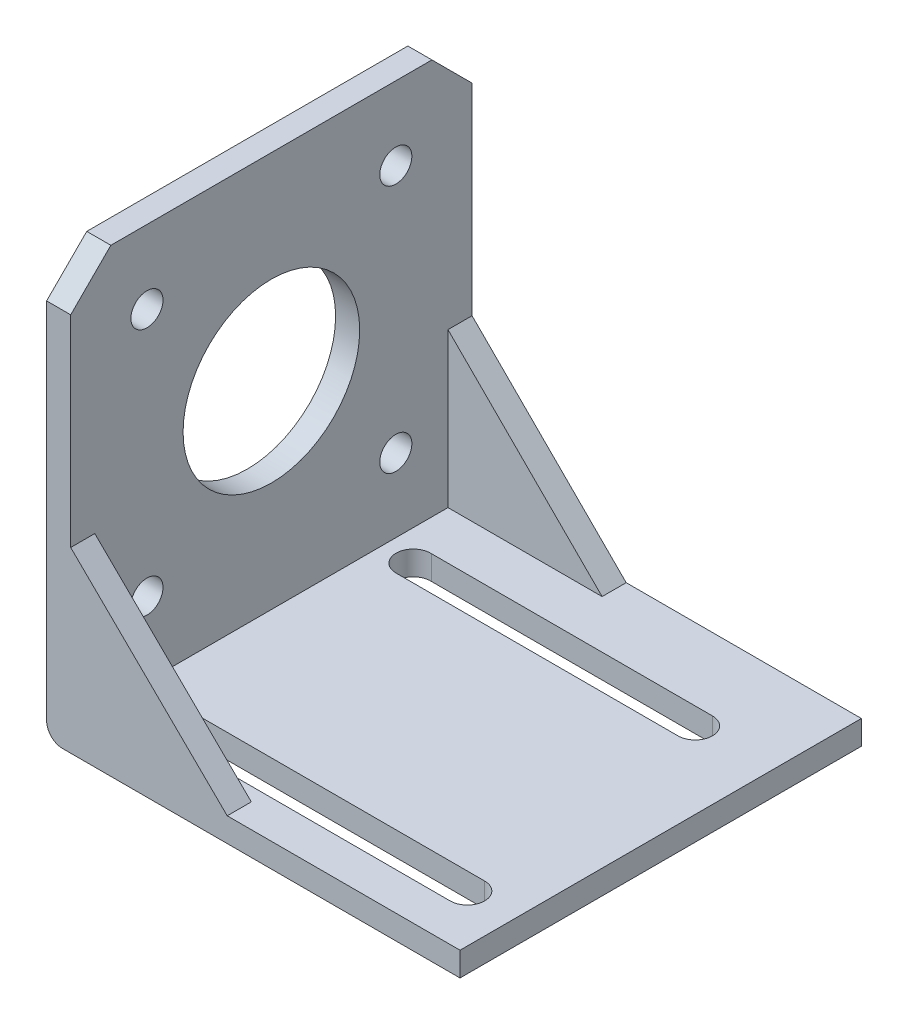
SolidWorks part; units mm, degrees
ref_plane "Front Plane" through (0, 0, 0) normal (0, 0, 1) x (1, 0, 0)
ref_plane "Top Plane" through (0, 0, 0) normal (0, 1, 0) x (1, 0, 0)
ref_plane "Right Plane" through (0, 0, 0) normal (1, 0, 0) x (0, 0, -1)
sketch "Sketch1" plane through (0, 0, 0) normal (0, 0, 1) x (1, 0, 0)
  line L0 (0, 0) -> (0, 49.3)
  line L1 (0, 49.3) -> (-3, 49.3)
  line L2 (-3, 49.3) -> (-3, -3)
  line L3 (-3, -3) -> (48.5, -3)
  line L4 (48.5, -3) -> (48.5, 0)
  line L5 (48.5, 0) -> (0, 0)
  dimension "D1" = 3
  dimension "D2" = 3
  dimension "D3" = 51.5
  dimension "D4" = 52.3
extrude "Boss-Extrude1" add sketch "Sketch1" along normal blind 50
sketch "Sketch8" plane through (0, 0, 50) normal (0, 0, 1) x (1, 0, 0)
  line L0 (0, 0) -> (0, 49.3) construction
  line L1 (48.5, 0) -> (0, 0) construction
  line L2 (-3, -3) -> (48.5, -3) construction
  line L3 (-3, 49.3) -> (-3, -3) construction
  line L4 (0, 19.2) -> (19.5, 0)
  point P0 (0, 19.2)
  point P1 (19.5, 0)
  dimension "D1" = 22.2
  dimension "D2" = 22.5
rib "Rib1" sketch "Sketch8" sketch "Sketch8" thickness 3 extrusion direction parallel to sketch draft on no parameters "D1"=3
sketch "Sketch10" plane through (0, 0, 0) normal (0, 0, 1) x (1, 0, 0)
  line L0 (0, 0) -> (0, 49.3) construction
  line L1 (48.5, 0) -> (0, 0) construction
  line L2 (-3, -3) -> (48.5, -3) construction
  line L3 (-3, 49.3) -> (-3, -3) construction
  line L4 (0, 19.2) -> (19.2, 0)
  point P0 (0, 19.2)
  point P1 (19.2, 0)
  dimension "D1" = 22.2
  dimension "D2" = 22.2
rib "Rib2" sketch "Sketch10" sketch "Sketch10" thickness 3 parameters "D1"=3
fillet "Fillet1" radius 2 1 edges at (-3, -3, 25)
sketch "Sketch11" plane through (0, 0, 0) normal (1, 0, 0) x (0, 0, -1)
  line L0 (-25, 0) -> (-25, 49.3) construction
  line L1 (-50, 0) -> (0, 0) construction
  line L2 (-50, 49.3) -> (0, 49.3) construction
  line L6 (-40.5, 38.15) -> (-40.5, 40.15)
  line L7 (-40.5, 9.15) -> (-9.5, 9.15)
  line L8 (-40.5, 9.15) -> (-40.5, 11.15)
  line L9 (-40.5, 40.15) -> (-38.5, 40.15)
  line L10 (-9.5, 9.15) -> (-9.5, 11.15)
  line L11 (-40.5, 9.15) -> (-39.0858, 10.5642) construction
  line L12 (-40.5, 40.15) -> (-39.0858, 38.7358) construction
  line L13 (-11.5, 40.15) -> (-9.5, 40.15)
  line L14 (-9.5, 38.15) -> (-9.5, 40.15)
  line L15 (-10.9142, 10.5642) -> (-9.5, 9.15) construction
  line L16 (-17.2218, 32.4282) -> (-9.5, 40.15) construction
  circle A0 centre (-25, 24.65) radius 11
  circle A1 centre (-40.5, 40.15) radius 2
  circle A2 centre (-9.5, 40.15) radius 2
  circle A3 centre (-9.5, 9.15) radius 2
  circle A4 centre (-40.5, 9.15) radius 2
  dimension "D1" = 22
  dimension "D4" = 4
  dimension "D5" = 4
  dimension "D6" = 4
  dimension "D7" = 4
  dimension "D2" = 31
  dimension "D3" = 31
extrude "Cut-Extrude1" cut sketch "Sketch11" against normal blind 50 contours A0 | A2 | A1 | A3 | A4
chamfer "Chamfer1" distance 5 angle 45 2 edges at (-1.5, 49.3, 0) (-1.5, 49.3, 50)
sketch "Sketch12" plane through (0, -3, 0) normal (0, -1, 0) x (1, 0, 0)
  line L0 (-1, 41) -> (62.7814, 41) construction
  line L1 (-1, 50) -> (-1, 0) construction
  line L2 (-1, 9) -> (65.5575, 9) construction
  line L3 (-1, 50) -> (48.5, 50) construction
  line L4 (-1, 0) -> (48.5, 0) construction
  line L5 (38.9492, 9) -> (3.928, 9)
  line L8 (38.9492, 13.3) -> (3.8289, 13.3)
  line L9 (3.0397, 41) -> (42.5714, 41)
  line L12 (3.0397, 45.3) -> (42.5714, 45.3)
  arc A0 (38.9492, 13.3) -> (38.9492, 9) centre (38.9492, 11.15) cw
  arc A1 (3.8289, 13.3) -> (3.928, 9) centre (3.8289, 11.1489) ccw
  arc A2 (3.0397, 45.3) -> (3.0397, 41) centre (3.0397, 43.15) ccw
  arc A3 (42.5714, 41) -> (42.5714, 45.3) centre (42.5714, 43.15) ccw
  dimension "D1" = 9
  dimension "D2" = 9
  dimension "D3" = 4.3
  dimension "D4" = 4.3
extrude "Cut-Extrude2" cut sketch "Sketch12" against normal blind 50
